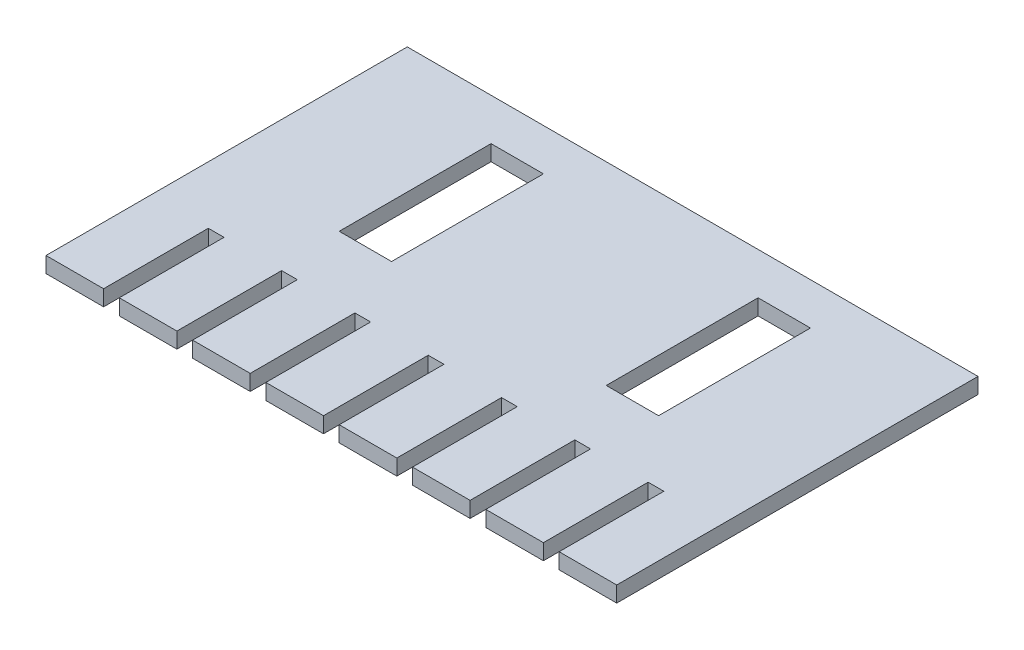
SolidWorks part; units mm, degrees
ref_plane "Front Plane" through (0, 0, 0) normal (0, 0, 1) x (1, 0, 0)
ref_plane "Top Plane" through (0, 0, 0) normal (0, 1, 0) x (1, 0, 0)
ref_plane "Right Plane" through (0, 0, 0) normal (1, 0, 0) x (0, 0, -1)
sketch "Sketch1" plane through (0, 0, 0) normal (0, 1, 0) x (1, 0, 0)
  line L1 (-27.25, 17.25) -> (27.25, 17.25)
  line L2 (-27.25, 17.25) -> (-27.25, -17.25)
  line L3 (-27.25, -17.25) -> (27.25, -17.25)
  line L4 (27.25, 17.25) -> (27.25, -17.25)
  line L5 (-27.25, 17.25) -> (27.25, -17.25) construction
  line L6 (-27.25, -17.25) -> (27.25, 17.25) construction
  point P0 (0, 0)
extrude "Boss-Extrude1" add sketch "Sketch1" along normal blind 1.5
sketch "Sketch2" plane through (0, 1.5, 0) normal (0, 1, 0) x (1, 0, 0)
  line L0 (0, 17.25) -> (0, 6)
  line L1 (27.25, 17.25) -> (-27.25, 17.25) construction
sketch "Sketch3" plane through (0, 1.5, 0) normal (0, 1, 0) x (1, 0, 0)
  line L0 (0, 6) -> (-27.25, 6)
  line L1 (-27.25, 17.25) -> (-27.25, -17.25) construction
sketch "Sketch5" plane through (0, 1.5, 0) normal (0, 1, 0) x (1, 0, 0)
  line L0 (-27.25, 6) -> (-12.75, 6)
sketch "Sketch6" plane through (0, 1.5, 0) normal (0, 1, 0) x (1, 0, 0)
  line L1 (-15.25, 13.25) -> (-10.25, 13.25)
  line L2 (-15.25, 13.25) -> (-15.25, -1.25)
  line L3 (-15.25, -1.25) -> (-10.25, -1.25)
  line L4 (-10.25, 13.25) -> (-10.25, -1.25)
  line L5 (-15.25, 13.25) -> (-10.25, -1.25) construction
  line L6 (-15.25, -1.25) -> (-10.25, 13.25) construction
  point P0 (-12.75, 6)
extrude "Cut-Extrude1" cut sketch "Sketch6" against normal blind 2
sketch "Sketch7" plane through (0, 1.5, 0) normal (0, 1, 0) x (1, 0, 0)
  line L0 (0, 6) -> (27.25, 6)
  line L1 (27.25, -17.25) -> (27.25, 17.25) construction
sketch "Sketch8" plane through (0, 1.5, 0) normal (0, 1, 0) x (1, 0, 0)
  line L0 (27.25, 6) -> (12.75, 6)
sketch "Sketch9" plane through (0, 1.5, 0) normal (0, 1, 0) x (1, 0, 0)
  line L1 (10.25, 13.25) -> (15.25, 13.25)
  line L2 (10.25, 13.25) -> (10.25, -1.25)
  line L3 (10.25, -1.25) -> (15.25, -1.25)
  line L4 (15.25, 13.25) -> (15.25, -1.25)
  line L5 (10.25, 13.25) -> (15.25, -1.25) construction
  line L6 (10.25, -1.25) -> (15.25, 13.25) construction
  point P0 (12.75, 6)
extrude "Cut-Extrude2" cut sketch "Sketch9" against normal blind 2
sketch "Sketch10" plane through (0, 1.5, 0) normal (0, 1, 0) x (1, 0, 0)
  line L0 (-27.25, -17.25) -> (-21.75, -17.25)
  line L1 (-27.25, -17.25) -> (27.25, -17.25) construction
sketch "Sketch11" plane through (0, 1.5, 0) normal (0, 1, 0) x (1, 0, 0)
  line L0 (-21.75, -17.25) -> (-20.25, -17.25)
  line L1 (-27.25, -17.25) -> (27.25, -17.25) construction
sketch "Sketch12" plane through (0, 1.5, 0) normal (0, 1, 0) x (1, 0, 0)
  line L0 (-20.25, -17.25) -> (-14.75, -17.25)
  line L1 (-27.25, -17.25) -> (27.25, -17.25) construction
sketch "Sketch13" plane through (0, 1.5, 0) normal (0, 1, 0) x (1, 0, 0)
  line L0 (-14.75, -17.25) -> (-13.25, -17.25)
  line L1 (-27.25, -17.25) -> (27.25, -17.25) construction
sketch "Sketch14" plane through (0, 1.5, 0) normal (0, 1, 0) x (1, 0, 0)
  line L0 (-13.25, -17.25) -> (-7.75, -17.25)
  line L1 (-27.25, -17.25) -> (27.25, -17.25) construction
sketch "Sketch15" plane through (0, 1.5, 0) normal (0, 1, 0) x (1, 0, 0)
  line L0 (-7.75, -17.25) -> (-6.25, -17.25)
  line L1 (-27.25, -17.25) -> (27.25, -17.25) construction
sketch "Sketch16" plane through (0, 1.5, 0) normal (0, 1, 0) x (1, 0, 0)
  line L0 (-6.25, -17.25) -> (-0.75, -17.25)
  line L1 (-27.25, -17.25) -> (27.25, -17.25) construction
sketch "Sketch17" plane through (0, 1.5, 0) normal (0, 1, 0) x (1, 0, 0)
  line L0 (-0.75, -17.25) -> (0.75, -17.25)
  line L1 (-27.25, -17.25) -> (27.25, -17.25) construction
sketch "Sketch18" plane through (0, 1.5, 0) normal (0, 1, 0) x (1, 0, 0)
  line L0 (0.75, -17.25) -> (6.25, -17.25)
  line L1 (-27.25, -17.25) -> (27.25, -17.25) construction
sketch "Sketch19" plane through (0, 1.5, 0) normal (0, 1, 0) x (1, 0, 0)
  line L0 (6.25, -17.25) -> (7.75, -17.25)
  line L1 (-27.25, -17.25) -> (27.25, -17.25) construction
sketch "Sketch20" plane through (0, 1.5, 0) normal (0, 1, 0) x (1, 0, 0)
  line L0 (7.75, -17.25) -> (13.25, -17.25)
  line L1 (-27.25, -17.25) -> (27.25, -17.25) construction
sketch "Sketch21" plane through (0, 1.5, 0) normal (0, 1, 0) x (1, 0, 0)
  line L0 (13.25, -17.25) -> (14.75, -17.25)
  line L1 (-27.25, -17.25) -> (27.25, -17.25) construction
sketch "Sketch22" plane through (0, 1.5, 0) normal (0, 1, 0) x (1, 0, 0)
  line L0 (14.75, -17.25) -> (20.25, -17.25)
  line L1 (-27.25, -17.25) -> (27.25, -17.25) construction
sketch "Sketch25" plane through (0, 1.5, 0) normal (0, 1, 0) x (1, 0, 0)
  line L0 (20.25, -17.25) -> (21.75, -17.25)
  line L1 (-27.25, -17.25) -> (27.25, -17.25) construction
  line L2 (21.75, -17.25) -> (27.25, -17.25)
sketch "Sketch27" plane through (0, 1.5, 0) normal (0, 1, 0) x (1, 0, 0)
  line L0 (-21.75, -17.25) -> (-21.75, -7.25)
  line L1 (-21.75, -7.25) -> (-20.25, -7.25)
  line L2 (-20.25, -7.25) -> (-20.25, -17.25)
  line L3 (-20.25, -17.25) -> (-21.75, -17.25)
extrude "Cut-Extrude3" cut sketch "Sketch27" against normal blind 2
sketch "Sketch28" plane through (0, 1.5, 0) normal (0, 1, 0) x (1, 0, 0)
  line L0 (-14.75, -17.25) -> (-14.75, -7.25)
  line L1 (-14.75, -7.25) -> (-13.25, -7.25)
  line L2 (-13.25, -7.25) -> (-13.25, -17.25)
  line L3 (-13.25, -17.25) -> (-14.75, -17.25)
extrude "Cut-Extrude4" cut sketch "Sketch28" against normal blind 2
sketch "Sketch29" plane through (0, 1.5, 0) normal (0, 1, 0) x (1, 0, 0)
  line L0 (-7.75, -17.25) -> (-7.75, -7.25)
  line L1 (-7.75, -7.25) -> (-6.25, -7.25)
  line L2 (-6.25, -7.25) -> (-6.25, -17.25)
  line L3 (-6.25, -17.25) -> (-7.75, -17.25)
extrude "Cut-Extrude5" cut sketch "Sketch29" against normal blind 2
sketch "Sketch30" plane through (0, 1.5, 0) normal (0, 1, 0) x (1, 0, 0)
  line L0 (-0.75, -17.25) -> (-0.75, -7.25)
  line L1 (-0.75, -7.25) -> (0.75, -7.25)
  line L2 (0.75, -7.25) -> (0.75, -17.25)
  line L3 (0.75, -17.25) -> (-0.75, -17.25)
extrude "Cut-Extrude6" cut sketch "Sketch30" against normal blind 2
sketch "Sketch31" plane through (0, 1.5, 0) normal (0, 1, 0) x (1, 0, 0)
  line L0 (6.25, -17.25) -> (6.25, -7.25)
  line L1 (6.25, -7.25) -> (7.75, -7.25)
  line L2 (7.75, -7.25) -> (7.75, -17.25)
  line L3 (7.75, -17.25) -> (6.25, -17.25)
extrude "Cut-Extrude7" cut sketch "Sketch31" against normal blind 2
sketch "Sketch32" plane through (0, 1.5, 0) normal (0, 1, 0) x (1, 0, 0)
  line L0 (13.25, -17.25) -> (13.25, -7.25)
  line L1 (13.25, -7.25) -> (14.75, -7.25)
  line L2 (14.75, -7.25) -> (14.75, -17.25)
  line L3 (14.75, -17.25) -> (13.25, -17.25)
extrude "Cut-Extrude8" cut sketch "Sketch32" against normal blind 2
sketch "Sketch33" plane through (0, 1.5, 0) normal (0, 1, 0) x (1, 0, 0)
  line L0 (20.25, -17.25) -> (20.25, -7.25)
  line L1 (20.25, -7.25) -> (21.75, -7.25)
  line L2 (21.75, -7.25) -> (21.75, -17.25)
  line L3 (21.75, -17.25) -> (20.25, -17.25)
extrude "Cut-Extrude9" cut sketch "Sketch33" against normal blind 2
sketch "Sketch36" plane through (0, 1.5, 0) normal (0, 1, 0) x (1, 0, 0)
  line L0 (21.75, -17.25) -> (26.75, -17.25)
  line L1 (21.75, -17.25) -> (27.25, -17.25) construction
